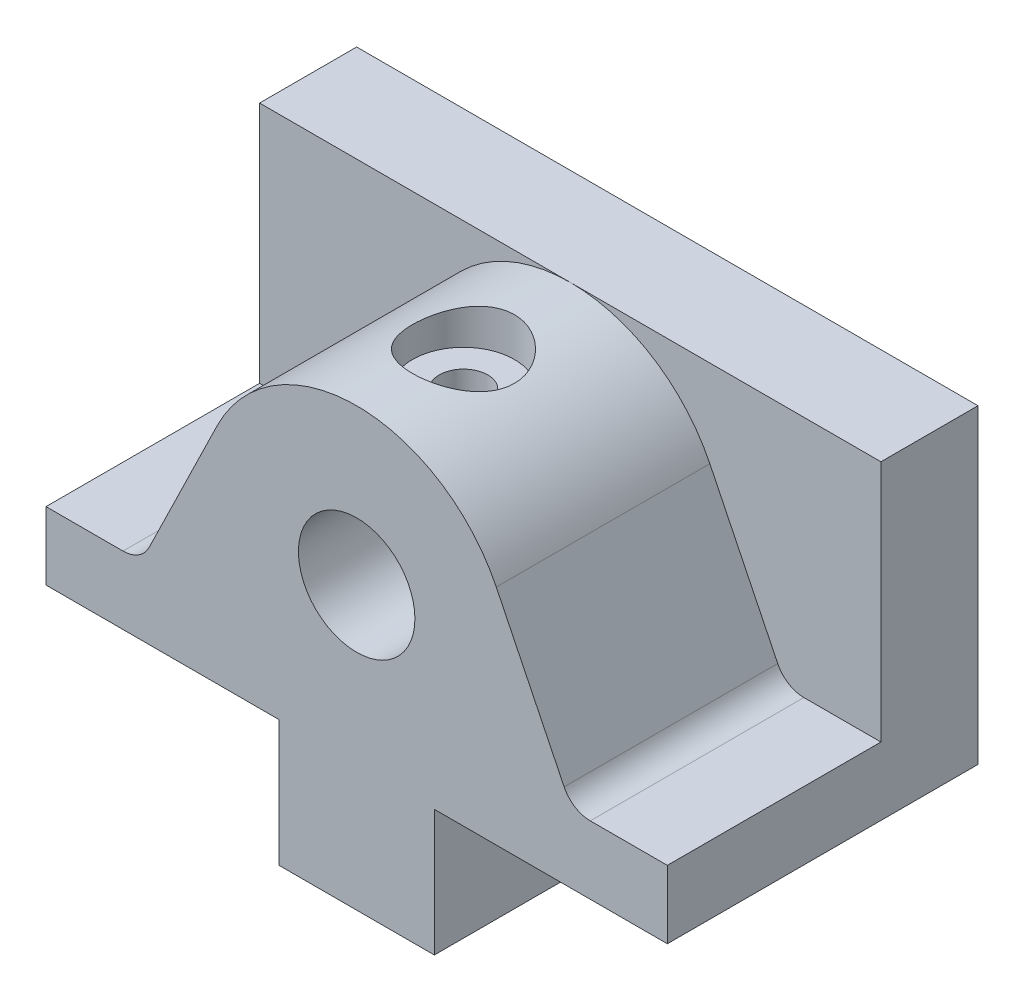
SolidWorks part; units mm, degrees
ref_plane "Ön Düzlem" through (0, 0, 0) normal (0, 0, 1) x (1, 0, 0)
ref_plane "Üst Düzlem" through (0, 0, 0) normal (0, 1, 0) x (1, 0, 0)
ref_plane "Sağ Düzlem" through (0, 0, 0) normal (1, 0, 0) x (0, 0, -1)
sketch "Çizim1" plane through (0, 0, 0) normal (0, 0, 1) x (1, 0, 0)
  line L0 (-37.139, 25.1349) -> (26.861, 25.1349)
  line L1 (26.861, 25.1349) -> (26.861, -6.8651)
  line L2 (26.861, -6.8651) -> (-37.139, -6.8651)
  line L3 (-37.139, -6.8651) -> (-37.139, 25.1349)
  dimension "D1" = 64
  dimension "D2" = 32
extrude "Yükseklik-Ekstrüzyon1" add sketch "Çizim1" along normal blind 32
sketch "Çizim2" plane through (0, 0, 32) normal (0, 0, 1) x (1, 0, 0)
  line L1 (-37.139, -6.8651) -> (26.861, -6.8651) construction
  line L2 (-5.139, -19.8651) -> (2.861, -19.8651)
  line L3 (2.861, -19.8651) -> (2.861, -6.8651)
  line L4 (2.861, -6.8651) -> (-5.139, -6.8651)
  line L5 (-13.139, -6.8651) -> (-13.139, -19.8651)
  line L6 (-13.139, -19.8651) -> (-5.139, -19.8651)
  line L7 (-13.139, -6.8651) -> (-5.139, -6.8651)
extrude "Yükseklik-Ekstrüzyon3" add sketch "Çizim2" against normal blind 32
sketch "Çizim3" plane through (0, 0, 32) normal (0, 0, 1) x (1, 0, 0)
  line L0 (-5.139, -19.8651) -> (-5.139, 9.1349)
  line L1 (-13.139, -19.8651) -> (2.861, -19.8651) construction
  line L2 (26.861, -6.8651) -> (26.861, 0.1349)
  line L3 (26.861, -6.8651) -> (26.861, 25.1349) construction
  line L4 (26.861, 0.1349) -> (-37.139, 0.1349)
  line L5 (-37.139, 25.1349) -> (-37.139, -6.8651) construction
  circle A0 centre (-5.139, 9.1349) radius 6
  circle A1 centre (-5.139, 9.1349) radius 16
  dimension "D1" = 7
extrude "Kes-Ekstrüzyon3" cut sketch "Çizim3" against normal blind 22
sketch "Çizim5" plane through (0, 0, 32) normal (0, 0, 1) x (1, 0, 0)
  line L0 (9.2417, 16.1489) -> (17.0522, 0.1349)
  line L1 (26.861, -6.8651) -> (26.861, 25.1349) construction
  line L2 (26.861, 0.1349) -> (17.0522, 0.1349)
  line L3 (-37.139, 25.1349) -> (-37.139, -6.8651) construction
  line L4 (-27.3302, 0.1349) -> (-37.139, 0.1349)
  line L5 (-19.5197, 16.1489) -> (-27.3302, 0.1349)
  line L6 (-37.139, 0.1349) -> (-37.139, 25.1349)
  line L7 (-37.139, 25.1349) -> (26.861, 25.1349)
  line L8 (26.861, 25.1349) -> (26.861, 0.1349)
  arc A0 (9.2417, 16.1489) -> (-19.5197, 16.1489) centre (-5.139, 9.1349) ccw
  line M5 (-37.139, 25.1349) -> (-37.139, -6.8651)
  line M11 (26.861, -6.8651) -> (26.861, 25.1349)
  line M12 (26.861, 25.1349) -> (-37.139, 25.1349)
extrude "Kes-Ekstrüzyon4" cut sketch "Çizim5" against normal blind 22 contours A0 L7 L4 L5 M5 | A0 L0 L2 M11 M12
fillet "Radyus1" radius 3 2 edges at (-27.3302, 0.1349, 21) (17.0522, 0.1349, 21)
sketch "Çizim6" plane through (0, 25.1349, 0) normal (0, 1, 0) x (1, 0, 0)
  circle A0 centre (-5.139, -21) radius 5.25
extrude "Kes-Ekstrüzyon5" cut sketch "Çizim6" against normal blind 4
hole_wizard "M6x1.0 Dişli Delik1" positions "3B Çizim1" profile "Çizim7" tap size "M6x1.0" standard "ANSI Metrik"
sketch3d "3B Çizim1"
  line L0 (-5.139, 21.1349, 21) -> (-5.139, 25.1349, 21) construction
  point P0 (-5.139, 21.1349, 21)
sketch "Çizim7" plane through (-5.139, 21.1349, 21) normal (1, 0, 0) x (0, 0, 1)
  line L0 (0, 0) -> (0, 6)
  line L1 (0, 6) -> (2.5, 6)
  line L2 (2.5, 6) -> (2.5, 0)
  line L5 (2.5, 0) -> (0, 0)
  line L11 (0, -6.35) -> (0, 107.95) construction
  dimension "Thru Tap Drill Dia." = 5
  dimension "Thru Tap Drill Depth" = 6
cosmetic thread "Delik Dişi1" parameters "D2"=6
sketch "Çizim10" plane through (0, -19.8651, 0) normal (0, -1, 0) x (-1, 0, 0)
  line L0 (5.139, -32) -> (5.139, 0) construction
  line L1 (13.139, -32) -> (-2.861, -32) construction
  line L2 (13.139, 0) -> (-2.861, 0) construction
hole_wizard "M6x1.0 Dişli Delik2" positions "3B Çizim3" profile "Çizim12" tap size "M6x1.0" standard "ANSI Metrik"
sketch3d "3B Çizim3"
  line L0 (-5.139, -19.8651, 32) -> (-5.139, -19.8651, 0) construction
  point P0 (-5.139, -19.8651, 24)
  point P4 (-5.139, -19.8651, 8)
  dimension "D1" = 8
  dimension "D2" = 8
sketch "Çizim12" plane through (-5.139, -19.8651, 24) normal (1, 0, 0) x (0, 0, -1)
  line L0 (0, 0) -> (0, 13.5022)
  line L1 (0, 13.5022) -> (2.5, 12)
  line L2 (2.5, 12) -> (2.5, 0)
  line L5 (2.5, 0) -> (0, 0)
  line L10 (0, 13.5022) -> (-2.5, 12) construction
  line L11 (0, -6.35) -> (0, 107.95) construction
  dimension "Tap Drill Dia." = 5
  dimension "Tap Drill Depth" = 12
  dimension "Drill Angle" = 118
cosmetic thread "Delik Dişi2" parameters "D1"=10, "D2"=6
cosmetic thread "Delik Dişi3" parameters "D1"=10, "D2"=6
